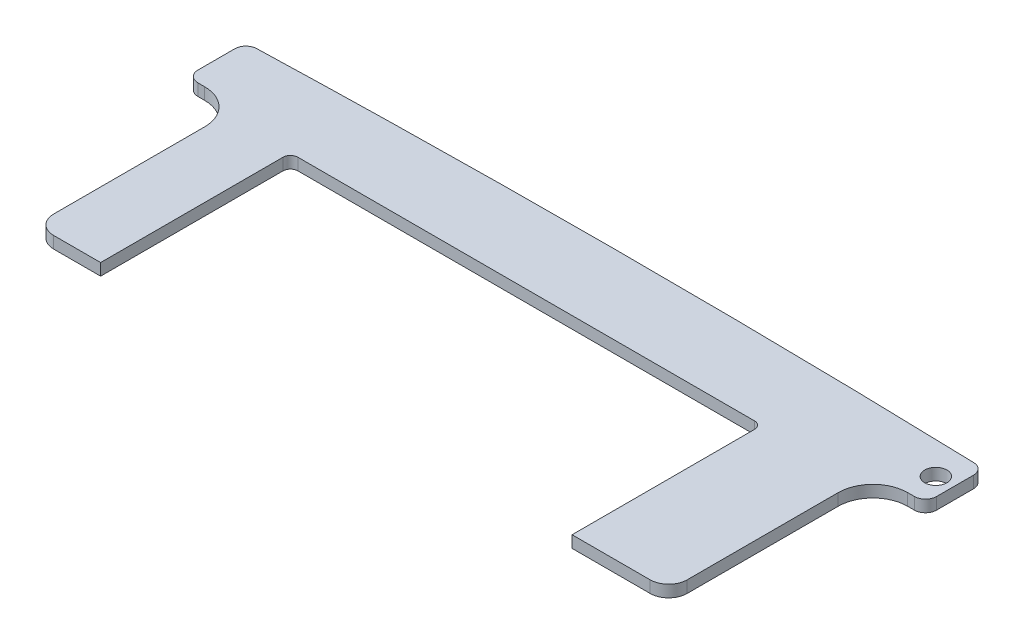
SolidWorks part; units mm, degrees
ref_plane "Front Plane" through (0, 0, 0) normal (0, 0, 1) x (1, 0, 0)
ref_plane "Top Plane" through (0, 0, 0) normal (0, 1, 0) x (1, 0, 0)
ref_plane "Right Plane" through (0, 0, 0) normal (1, 0, 0) x (0, 0, -1)
sketch "Sketch1" plane through (0, 0, 0) normal (0, 1, 0) x (1, 0, 0)
  line L18 (0.9, -3.8) -> (0, -3.8)
  line L20 (-7.2, -31.4019) -> (-17.75, -31.4019)
  line L22 (-4.7, -8.5) -> (-4.7, -28.9019)
  line L24 (-17.75, -31.4019) -> (-17.75, -5.7519)
  line L39 (-17.75, -5.7519) -> (-81.45, -5.7519)
  line L40 (-81.45, -5.7519) -> (-81.45, -31.4019)
  line L42 (-82.45, -4.7519) -> (-82.45, -52.5519) construction
  line L43 (-16.75, -4.7519) -> (-82.45, -4.7519) construction
  line L44 (-16.75, -24.5519) -> (-16.75, -4.7519) construction
  line L47 (-47.5, -2.3) -> (2.4, -2.3) construction
  line L48 (-90.3, -28.9019) -> (-90.3, -8.5)
  line L49 (-90.5, -26.4019) -> (-90.5, -8.5) construction
  line L54 (-95, -3.8) -> (-95.9, -3.8)
  line L55 (-97.4, 2.6764) -> (-97.4, -2.3)
  line L56 (-95, -4) -> (-97, -4) construction
  line L147 (-81.45, -31.4019) -> (-87.8, -31.4019)
  line L149 (2.4, -2.3) -> (2.4, 2.6764)
  circle A0 centre (0, 0) radius 1.5
  arc A15 (0, -3.8) -> (-4.7, -8.5) centre (0, -8.5) ccw
  arc A17 (0, -4) -> (-4.5, -8.5) centre (0, -8.5) ccw construction
  arc A19 (0, -4) -> (-4.5, -8.5) centre (0, -8.5) ccw construction
  arc A21 (-4.7, -28.9019) -> (-7.2, -31.4019) centre (-7.2, -28.9019) cw
  arc A37 (-87.8, -31.4019) -> (-90.3, -28.9019) centre (-87.8, -28.9019) cw
  arc A41 (-90.3, -8.5) -> (-95, -3.8) centre (-95, -8.5) ccw
  arc A42 (-90.5, -8.5) -> (-95, -4) centre (-95, -8.5) ccw construction
  arc A43 (-95.9, -3.8) -> (-97.4, -2.3) centre (-95.9, -2.3) cw
  arc A44 (-97.4, 2.6764) -> (-95.945, 4.1757) centre (-95.9, 2.6764) cw
  arc A147 (0.9, -3.8) -> (2.4, -2.3) centre (0.9, -2.3) ccw
  arc A148 (2.4, 2.6764) -> (0.945, 4.1757) centre (0.9, 2.6764) ccw
  ellipse E0 centre (-47.5, -49.6315) end of major axis (-346.0956, -49.6315) minor radius 54.5297 (0.945, 4.1757) -> (-95.945, 4.1757) ccw
  spline S0 degree 2 poles (-96.1038, 4.0122) (-93.1748, 4.1219) (-87.4351, 4.3243) (-80.9429, 4.5352) (-74.3439, 4.7228) (-66.8513, 4.902) (-57.4597, 5.0563) (-47.5, 5.1121) (-37.5403, 5.0563) (-28.1487, 4.902) (-20.6561, 4.7228) (-14.0571, 4.5352) (-7.5649, 4.3243) (-1.8252, 4.1219) (1.1038, 4.0122) knots 0.099097 0.099097 0.099097 0.131803 0.169892 0.220678 0.271464 0.347643 0.449214 0.550786 0.652357 0.728536 0.779322 0.830108 0.868197 0.900903 0.900903 0.900903 construction
  spline S1 degree 2 poles (-97.0755, 3.9757) (-93.6113, 4.1065) (-87.4351, 4.3243) (-80.9429, 4.5352) (-74.3439, 4.7228) (-66.8513, 4.902) (-57.4597, 5.0563) (-47.5, 5.1121) (-37.5403, 5.0563) (-28.1487, 4.902) (-20.6561, 4.7228) (-14.0571, 4.5352) (-7.5649, 4.3243) (-1.3887, 4.1065) (2.0755, 3.9757) knots 0.093714 0.093714 0.093714 0.131803 0.169892 0.220678 0.271464 0.347643 0.449214 0.550786 0.652357 0.728536 0.779322 0.830108 0.868197 0.906286 0.906286 0.906286 construction
  point P7 (-47.5, 1.1318)
  point P58 (-47.5, 5.0981)
  dimension "D1" = 3
  dimension "D7" = 1.5
  dimension "D8" = 1.5
  dimension "D10" = 1
  dimension "D11" = 0.2
  dimension "D3" = 0.2
  dimension "D9" = 2.5
  dimension "D12" = 49.9
  dimension "D13" = 1.5
  dimension "D14" = 1.5
  dimension "D17" = 2.5
  dimension "D4" = 1
  dimension "D5" = 1
  dimension "D6" = 49.9
  dimension "D2" = 0.2
  dimension "D15" = 0.2
  dimension "D16" = 0.2
  dimension "D18" = 25.65
extrude "Boss-Extrude1" add sketch "Sketch1" along normal blind 1.6
sketch "Sketch2" plane through (0, 1.6, 0) normal (0, 1, 0) x (1, 0, 0)
  point P0 (-86.5, -12.9019)
  point P1 (-86.5, -18.9019)
  point P3 (-86.5, -24.9019)
  point P5 (-95, 0)
  point P7 (-88.2184, 0.3002)
  point P9 (-81.4349, 0.5543)
  point P11 (-74.6498, 0.7622)
  point P13 (-67.8634, 0.9239)
  point P15 (-61.0761, 1.0394)
  point P17 (-54.2882, 1.1087)
  point P19 (-47.5, 1.1318)
  point P21 (-40.7118, 1.1087)
  point P23 (-33.9239, 1.0394)
  point P25 (-27.1366, 0.9239)
  point P27 (-20.3502, 0.7622)
  point P29 (-13.5651, 0.5543)
  point P31 (-6.7816, 0.3002)
  point P33 (-8.5, -12.9019)
  point P35 (-8.5, -18.9019)
  point P37 (-8.5, -24.9019)
  point P41 (0, 0)
fillet "Fillet1" radius 1 2 edges at (-81.45, 0.8, 5.7519) (-17.75, 0.8, 5.7519)
